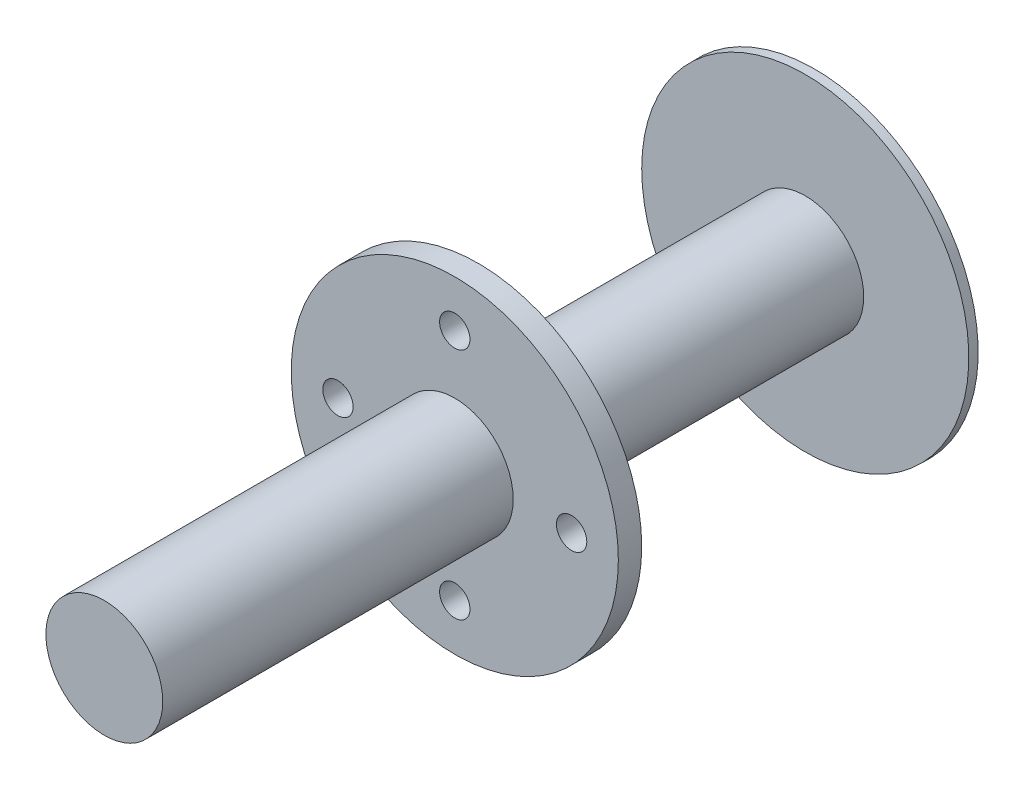
SolidWorks part; units mm, degrees
ref_plane "Front Plane" through (0, 0, 0) normal (0, 0, 1) x (1, 0, 0)
ref_plane "Top Plane" through (0, 0, 0) normal (0, 1, 0) x (1, 0, 0)
ref_plane "Right Plane" through (0, 0, 0) normal (1, 0, 0) x (0, 0, -1)
sketch "Sketch1" plane through (0, 0, 0) normal (0, 0, 1) x (1, 0, 0)
  circle A0 centre (0, 0) radius 70
  circle A1 centre (0, 50) radius 6.5
  circle A2 centre (50, 0) radius 6.5
  circle A3 centre (0, -50) radius 6.5
  circle A4 centre (-50, 0) radius 6.5
  point P5 (-38.5005, -10.8731)
  point P6 (0, 0)
  point P14 (0, 0)
  dimension "D1" = 140
  dimension "D2" = 13
  dimension "D3" = 50
  dimension "D4" = 4
extrude "Boss-Extrude1" add sketch "Sketch1" along normal blind 10
sketch "Sketch2" plane through (0, 0, 10) normal (0, 0, 1) x (1, 0, 0)
  circle A0 centre (0, 0) radius 25
  dimension "D1" = 50
extrude "Boss-Extrude2" add sketch "Sketch2" along normal blind 150 and the other way blind 150
sketch "Sketch3" plane through (0, 0, -140) normal (0, 0, -1) x (-1, 0, 0)
  circle A0 centre (0, 0) radius 70 construction
  circle A1 centre (0, 0) radius 70
extrude "Boss-Extrude3" add sketch "Sketch3" along normal blind 4
